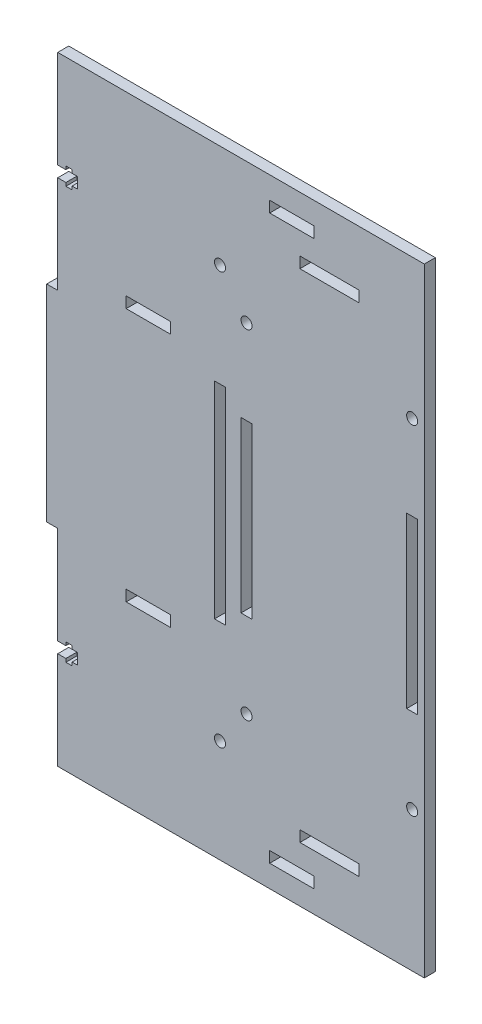
SolidWorks part; units mm, degrees
ref_plane "Alzado" through (0, 0, 0) normal (0, 0, 1) x (1, 0, 0)
ref_plane "Planta" through (0, 0, 0) normal (0, 1, 0) x (1, 0, 0)
ref_plane "Vista lateral" through (0, 0, 0) normal (1, 0, 0) x (0, 0, -1)
sketch "Croquis1" plane through (0, 0, 0) normal (0, 0, 1) x (1, 0, 0)
  line L0 (68, 280) -> (68, 236.7398) construction
  line L1 (0, 0) -> (136, 0)
  line L2 (0, 0) -> (0, 280)
  line L3 (0, 280) -> (136, 280)
  line L4 (136, 0) -> (136, 280)
  line L5 (0, 280) -> (5, 280)
  line L6 (0, 280) -> (0, 0)
  line L7 (0, 0) -> (5, 0)
  line L8 (5, 280) -> (5, 0)
  line L9 (131, 280) -> (131, 0)
  line L10 (0, 186.6667) -> (5, 186.6667)
  line L11 (5, 93.3333) -> (0, 93.3333)
  line L12 (131, 93.3333) -> (136, 93.3333)
  line L13 (136, 186.6667) -> (131, 186.6667)
  line L14 (0, 140) -> (16.4555, 140) construction
  dimension "D1" = 280
  dimension "D2" = 136
  dimension "D3" = 5
  dimension "D4" = 93.3333
  dimension "D5" = 93.3333
extrude "Saliente-Extruir1" add sketch "Croquis1" along normal blind 5 contours L9 L3 L8 L1 | L11 L8 L10 L6
sketch "Croquis2" plane through (0, 0, 5) normal (0, 0, 1) x (1, 0, 0)
  line L0 (5, 233.3333) -> (14, 233.3333) construction
  line L1 (5, 280) -> (5, 186.6667) construction
  line L2 (68, 280) -> (68, 267.6992)
  line L3 (5, 280) -> (131, 280) construction
  line L4 (0, 140) -> (9.7749, 140)
  line L5 (0, 93.3333) -> (0, 186.6667) construction
  line L6 (5, 235.8333) -> (8.7, 235.8333)
  line L7 (8.7, 235.8333) -> (8.7, 237.3333)
  line L8 (8.7, 237.3333) -> (11.5, 237.3333)
  line L9 (11.5, 237.3333) -> (11.5, 235.8333)
  line L10 (11.5, 235.8333) -> (14, 235.8333)
  line L11 (14, 235.8333) -> (14, 230.8333)
  line L12 (11.5, 230.8333) -> (14, 230.8333)
  line L13 (11.5, 229.3333) -> (11.5, 230.8333)
  line L14 (8.7, 229.3333) -> (11.5, 229.3333)
  line L15 (8.7, 230.8333) -> (8.7, 229.3333)
  line L16 (5, 230.8333) -> (8.7, 230.8333)
  line L17 (131, 233.3333) -> (122, 233.3333) construction
  line L18 (131, 230.8333) -> (127.3, 230.8333)
  line L19 (127.3, 230.8333) -> (127.3, 229.3333)
  line L20 (127.3, 229.3333) -> (124.5, 229.3333)
  line L21 (124.5, 229.3333) -> (124.5, 230.8333)
  line L22 (124.5, 230.8333) -> (122, 230.8333)
  line L23 (122, 235.8333) -> (122, 230.8333)
  line L24 (124.5, 235.8333) -> (122, 235.8333)
  line L25 (124.5, 237.3333) -> (124.5, 235.8333)
  line L26 (127.3, 237.3333) -> (124.5, 237.3333)
  line L27 (127.3, 235.8333) -> (127.3, 237.3333)
  line L28 (131, 235.8333) -> (127.3, 235.8333)
  line L29 (131, 46.6667) -> (122, 46.6667) construction
  line L30 (5, 46.6667) -> (14, 46.6667) construction
  line L31 (131, 44.1667) -> (127.3, 44.1667)
  line L32 (127.3, 44.1667) -> (127.3, 42.6667)
  line L33 (127.3, 42.6667) -> (124.5, 42.6667)
  line L34 (124.5, 42.6667) -> (124.5, 44.1667)
  line L35 (124.5, 44.1667) -> (122, 44.1667)
  line L36 (122, 44.1667) -> (122, 49.1667)
  line L37 (124.5, 49.1667) -> (122, 49.1667)
  line L38 (124.5, 50.6667) -> (124.5, 49.1667)
  line L39 (127.3, 50.6667) -> (124.5, 50.6667)
  line L40 (127.3, 49.1667) -> (127.3, 50.6667)
  line L41 (131, 49.1667) -> (127.3, 49.1667)
  line L42 (5, 49.1667) -> (8.7, 49.1667)
  line L43 (8.7, 49.1667) -> (8.7, 50.6667)
  line L44 (8.7, 50.6667) -> (11.5, 50.6667)
  line L45 (11.5, 50.6667) -> (11.5, 49.1667)
  line L46 (11.5, 49.1667) -> (14, 49.1667)
  line L47 (14, 44.1667) -> (14, 49.1667)
  line L48 (11.5, 44.1667) -> (14, 44.1667)
  line L49 (11.5, 42.6667) -> (11.5, 44.1667)
  line L50 (8.7, 42.6667) -> (11.5, 42.6667)
  line L51 (8.7, 44.1667) -> (8.7, 42.6667)
  line L52 (5, 44.1667) -> (8.7, 44.1667)
  line M12 (5, 280) -> (5, 186.6667)
  line M16 (5, 93.3333) -> (5, 0)
  dimension "D1" = 2.5
  dimension "D2" = 4
  dimension "D3" = 2.8
  dimension "D4" = 9
  dimension "D5" = 3.7
extrude "Cortar-Extruir1" cut sketch "Croquis2" against normal blind 5 contours L16 L15 L14 L13 L12 L11 L10 L9 L8 L7 L6 M12 | L52 L51 L50 L49 L48 L47 L46 L45 L44 L43 L42 M16
sketch "Croquis3" plane through (0, 0, 5) normal (0, 0, 1) x (1, 0, 0)
  line L0 (5, 280) -> (131, 280) construction
  line L1 (76, 280) -> (81, 280)
  line L2 (76, 280) -> (76, 0)
  line L3 (76, 0) -> (81, 0)
  line L4 (81, 280) -> (81, 0)
  line L5 (5, 0) -> (131, 0) construction
  line L6 (5, 280) -> (5, 235.8333) construction
  line L7 (76, 186.6667) -> (81, 186.6667)
  line L8 (76, 93.3333) -> (81, 93.3333)
  point P10 (5, 257.9167)
  point P13 (78.5, 186.6667)
  dimension "D1" = 71
  dimension "D2" = 5
  dimension "D3" = 93.3333
  dimension "D4" = 93.3333
extrude "Cortar-Extruir2" cut sketch "Croquis3" against normal blind 5 contours L2 L8 L4 L7
sketch "Croquis4" plane through (0, 0, 5) normal (0, 0, 1) x (1, 0, 0)
  line L0 (78.5, 186.6667) -> (78.5, 280) construction
  line L1 (76, 186.6667) -> (81, 186.6667) construction
  line L2 (5, 280) -> (131, 280) construction
  line L3 (78.5, 93.3333) -> (78.5, 0) construction
  line L5 (76, 93.3333) -> (81, 93.3333) construction
  line L6 (5, 0) -> (131, 0) construction
  circle A0 centre (78.5, 233.3333) radius 2.5
  circle A1 centre (78.5, 46.6667) radius 2.5
  dimension "D1" = 5
extrude "Cortar-Extruir3" cut sketch "Croquis4" against normal blind 5
sketch "Croquis5" plane through (0, 0, 5) normal (0, 0, 1) x (1, 0, 0)
  line L0 (76, 280) -> (76, 0) construction
  line L1 (76, 186.6667) -> (76, 93.3333) construction
  line L2 (5, 0) -> (131, 0) construction
  line L3 (76, 140) -> (83.8361, 140) construction
  line L4 (76, 200) -> (36, 200)
  line L5 (76, 200) -> (76, 195)
  line L6 (76, 195) -> (36, 195)
  line L7 (36, 200) -> (36, 195)
  line L8 (0, 93.3333) -> (0, 186.6667) construction
  line L9 (76, 270) -> (121, 270)
  line L10 (76, 270) -> (76, 265)
  line L11 (76, 265) -> (121, 265)
  line L12 (121, 270) -> (121, 265)
  line L13 (56, 195) -> (56, 200)
  line L14 (101, 270) -> (101, 265)
  line L15 (101, 10) -> (101, 15)
  line L16 (56, 85) -> (56, 80)
  line L17 (121, 10) -> (121, 15)
  line L18 (76, 15) -> (121, 15)
  line L19 (76, 10) -> (76, 15)
  line L20 (76, 10) -> (121, 10)
  line L21 (36, 80) -> (36, 85)
  line L22 (76, 85) -> (36, 85)
  line L23 (76, 80) -> (76, 85)
  line L24 (76, 80) -> (36, 80)
  point P7 (76, 140)
  point P21 (0, 140)
  point P24 (101, 267.5)
  dimension "D1" = 5
  dimension "D2" = 5
  dimension "D3" = 60
  dimension "D4" = 45
  dimension "D5" = 40
  dimension "D6" = 70
  dimension "D7" = 20
extrude "Cortar-Extruir4" cut sketch "Croquis5" against normal blind 5
sketch "Croquis6" plane through (0, 0, 5) normal (0, 0, 1) x (1, 0, 0)
  line L0 (5, 0) -> (131, 0) construction
  line L1 (131, 280) -> (171, 280)
  line L2 (131, 280) -> (131, 0)
  line L3 (131, 0) -> (171, 0)
  line L4 (171, 280) -> (171, 0)
  dimension "D1" = 40
extrude "Saliente-Extruir2" add sketch "Croquis6" against normal blind 5
sketch "Croquis7" plane through (0, 0, 5) normal (0, 0, 1) x (1, 0, 0)
  line L0 (93, 250) -> (93, 30)
  line L1 (93, 30) -> (163, 30)
  line L2 (163, 30) -> (163, 250)
  line L3 (163, 250) -> (93, 250)
  line L4 (88, 255) -> (88, 25)
  line L5 (88, 25) -> (168, 25)
  line L6 (168, 25) -> (168, 255)
  line L7 (168, 255) -> (88, 255)
  line L8 (5, 0) -> (171, 0) construction
  line L9 (81, 186.6667) -> (81, 93.3333) construction
  line L10 (93, 250) -> (93, 255)
  line L11 (93, 30) -> (93, 25)
  line L12 (163, 30) -> (163, 25)
  line L13 (163, 250) -> (163, 255)
  line L14 (5, 280) -> (171, 280) construction
  line L16 (88, 178.3333) -> (93, 178.3333)
  line L17 (93, 101.6667) -> (88, 101.6667)
  line L18 (163, 178.3333) -> (168, 178.3333)
  line L19 (163, 101.6667) -> (168, 101.6667)
  line L20 (88, 216.6667) -> (93, 216.6667) construction
  line L21 (128, 255) -> (128, 151.4654) construction
  line L22 (163, 140) -> (153.4822, 140) construction
  line L23 (114.6667, 255) -> (114.6667, 250)
  line L24 (141.3333, 255) -> (141.3333, 250)
  line L25 (141.3333, 25) -> (141.3333, 30)
  line L26 (114.6667, 25) -> (114.6667, 30)
  circle A0 centre (90.5, 216.6667) radius 2.5
  circle A1 centre (165.5, 216.6667) radius 2.5
  circle A2 centre (165.5, 63.3333) radius 2.5
  circle A3 centre (90.5, 63.3333) radius 2.5
  dimension "D9" = 5
  dimension "D2" = 70
  dimension "D4" = 30
  dimension "D5" = 12
  dimension "D6" = 76.6667
  dimension "D7" = 76.6667
  dimension "D8" = 38.3333
  dimension "D10" = 26.6667
  dimension "D11" = 26.6667
  dimension "D12" = 30
  dimension "D3" = 5
extrude "Cortar-Extruir5" cut sketch "Croquis7" against normal blind 5 contours L17 L0 L16 L4 | L2 L19 L6 L18 | L26 L5 L25 L1 | L24 L7 L23 L3 | A0 | A1 | A2 | A3
